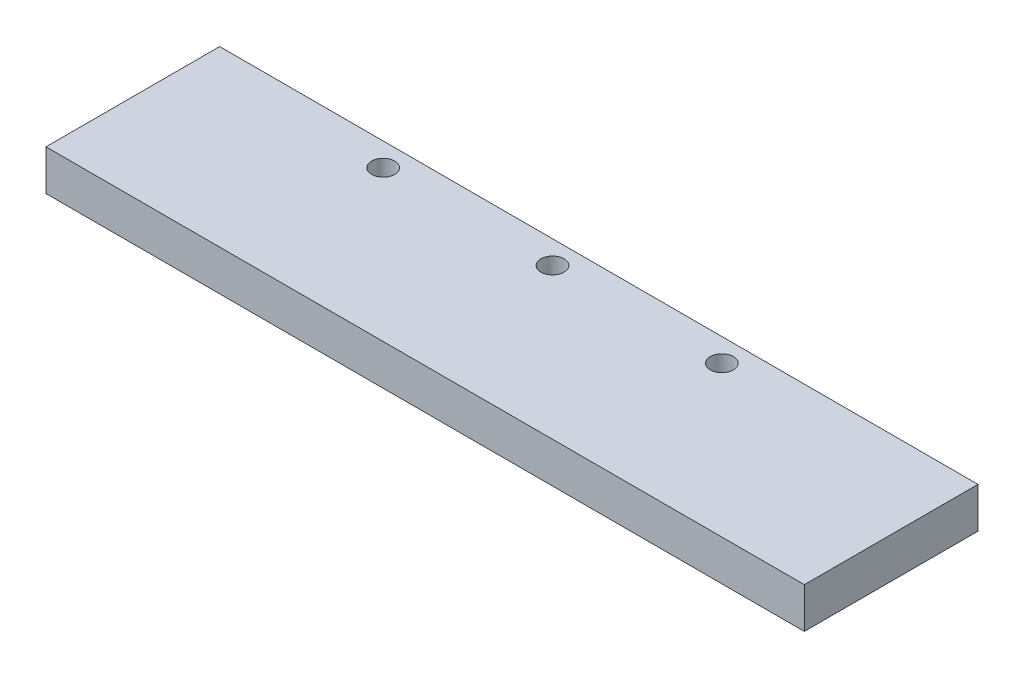
SolidWorks part; units mm, degrees
ref_plane "Front Plane" through (0, 0, 0) normal (0, 0, 1) x (1, 0, 0)
ref_plane "Top Plane" through (0, 0, 0) normal (0, 1, 0) x (1, 0, 0)
ref_plane "Right Plane" through (0, 0, 0) normal (1, 0, 0) x (0, 0, -1)
sketch "Sketch1" plane through (0, 0, 0) normal (0, 1, 0) x (1, 0, 0)
  line L1 (-102.5105, 65.1674) -> (28.4895, 65.1674)
  line L2 (-102.5105, 65.1674) -> (-102.5105, 35.1674)
  line L3 (-102.5105, 35.1674) -> (28.4895, 35.1674)
  line L4 (28.4895, 65.1674) -> (28.4895, 35.1674)
  dimension "D1" = 30
  dimension "D2" = 131
extrude "Boss-Extrude1" add sketch "Sketch1" along normal blind 7 contours L2 L3 L4 L1
sketch "Sketch2" plane through (0, 0, 0) normal (0, -1, 0) x (1, 0, 0)
  line L0 (-102.5105, -65.1674) -> (-102.5105, -35.1674) construction
  line L1 (-102.5105, -65.1674) -> (28.4895, -65.1674) construction
  circle A0 centre (-70.2605, -61.1674) radius 2
  circle A1 centre (-41.0105, -61.1674) radius 2
  circle A2 centre (-11.7605, -61.1674) radius 2
  dimension "D1" = 32.25
  dimension "D5" = 29.25
  dimension "D2" = 4
  dimension "D3" = 29.25
  dimension "D4" = 4
  dimension "D6" = 4
extrude "Cut-Extrude1" cut sketch "Sketch2" against normal blind 10
